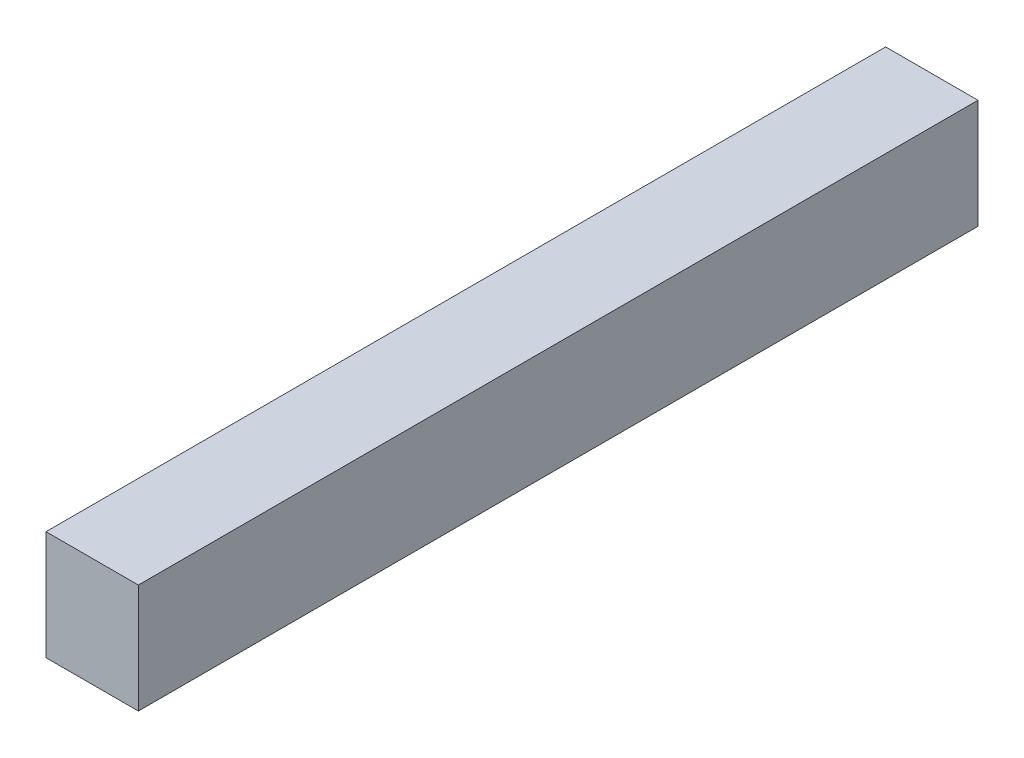
SolidWorks part; units mm, degrees
ref_plane "Front Plane" through (0, 0, 0) normal (0, 0, 1) x (1, 0, 0)
ref_plane "Top Plane" through (0, 0, 0) normal (0, 1, 0) x (1, 0, 0)
ref_plane "Right Plane" through (0, 0, 0) normal (1, 0, 0) x (0, 0, -1)
sketch "Sketch1" plane through (0, 0, 0) normal (0, 0, 1) x (1, 0, 0)
  line L1 (-1.375, 1.625) -> (1.375, 1.625)
  line L2 (-1.375, 1.625) -> (-1.375, -1.625)
  line L3 (-1.375, -1.625) -> (1.375, -1.625)
  line L4 (1.375, 1.625) -> (1.375, -1.625)
  line L5 (-1.375, 1.625) -> (1.375, -1.625) construction
  line L6 (-1.375, -1.625) -> (1.375, 1.625) construction
  point P0 (0, 0)
  dimension "D1" = 2.75
  dimension "D2" = 3.25
extrude "Boss-Extrude1" add sketch "Sketch1" along normal blind 25
